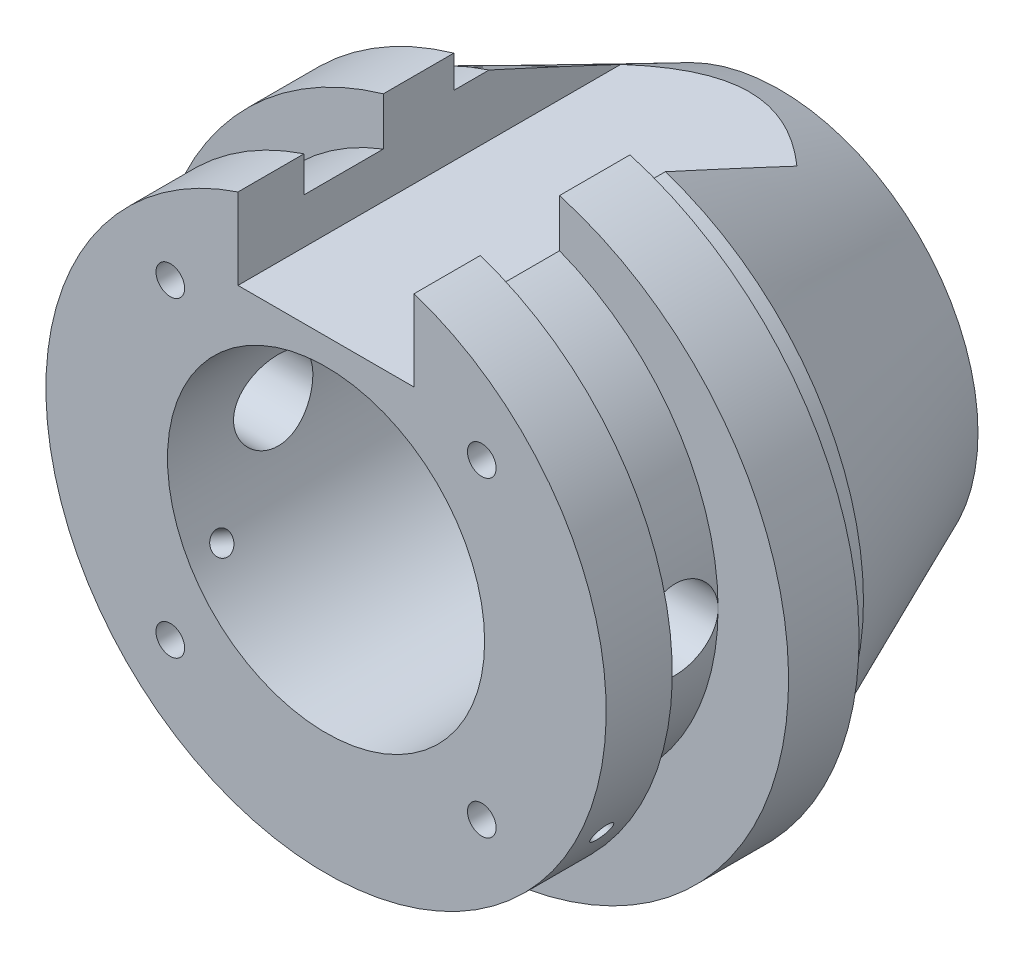
SolidWorks part; units mm, degrees
ref_plane "Plane1" through (0, 0, 0) normal (0, 0, 1) x (1, 0, 0)
ref_plane "Plane2" through (0, 0, 0) normal (0, 1, 0) x (1, 0, 0)
ref_plane "Plane3" through (0, 0, 0) normal (1, 0, 0) x (0, 0, -1)
sketch "Esquisse1" plane through (0, 0, 0) normal (0, 0, 1) x (1, 0, 0)
  circle A0 centre (0, 0) radius 36
  dimension "D1" = 72
extrude "Base-Extrusion" add sketch "Esquisse1" along normal blind 8
sketch "Esquisse2" plane through (0, 0, 0) normal (0, 0, -1) x (-1, 0, 0)
  circle A0 centre (0, 0) radius 32.5
  dimension "D1" = 65
extrude "Boss.-Extru.1" add sketch "Esquisse2" along normal blind 4
sketch "Esquisse3" plane through (0, 0, 0) normal (1, 0, 0) x (0, 0, -1)
  line L0 (4, 32.5) -> (27, 22.4993)
  line L1 (4, -32.5) -> (4, 32.5) construction
  line L2 (27, 22.4993) -> (27, 0)
  line L3 (0, 0) -> (39.1583, 0) construction
  line L4 (-8, 0) -> (0, 0) construction
  line L5 (4, 32.5) -> (4, 0)
  line L6 (4, 0) -> (27, 0)
  dimension "D1" = 23.5
  dimension "D2" = 23
revolve "Boss.-Révol.1" add sketch "Esquisse3" angle 360 about L3
sketch "Esquisse4" plane through (0, 0, 8) normal (0, 0, 1) x (1, 0, 0)
  line L0 (0, 0) -> (0, 21.3127) construction
  circle A0 centre (0, 3) radius 28
  dimension "D1" = 56
  dimension "D2" = 3
extrude "Boss.-Extru.2" add sketch "Esquisse4" along normal blind 9
sketch "Esquisse5" plane through (0, 0, 17) normal (0, 0, 1) x (1, 0, 0)
  circle A0 centre (0, 3) radius 31.8
  dimension "D1" = 63.6
extrude "Boss.-Extru.3" add sketch "Esquisse5" along normal blind 7.5
sketch "Esquisse6" plane through (0, 0, 24.5) normal (0, 0, 1) x (1, 0, 0)
  circle A0 centre (0, 3) radius 18
  dimension "D1" = 36
extrude "Enlèv. mat.-Extru.1" cut sketch "Esquisse6" against normal through all
sketch "Esquisse10" plane through (0, 0, 24.5) normal (0, 0, 1) x (1, 0, 0)
  line L0 (-10, 38.61) -> (10, 38.61)
  line L1 (-10, 38.61) -> (-10, 24)
  line L2 (10, 24) -> (-10, 24)
  line L3 (10, 24) -> (10, 38.61)
  line L4 (0, 0) -> (0, 38.61) construction
  line L5 (0, 3) -> (7.9537, 3) construction
  dimension "D1" = 21
  dimension "D2" = 20
extrude "Enlèv. mat.-Extru.5" cut sketch "Esquisse10" against normal through all
hole_wizard "Perçage1" positions "Esquisse12" profile "Esquisse11" legacy
sketch "Esquisse12" plane through (0, 0, 24.5) normal (0, 0, 1) x (1, 0, 0)
  line L0 (0, 3) -> (0, 12.7663) construction
  line L1 (0, 3) -> (22.3317, 3) construction
  line L2 (0, 3) -> (-17.6777, 20.6777) construction
  point P0 (-17.6777, 20.6777)
  dimension "D1" = 25
  dimension "D2" = 45
sketch "Esquisse11" plane through (-17.6777, 20.6777, 24.5) normal (1, 0, 0) x (0, -1, 0)
  line L0 (0, 0) -> (0, 12.9764)
  line L1 (0, 12.9764) -> (1.625, 12)
  line L2 (1.625, 12) -> (1.625, 0)
  line L4 (1.625, 0) -> (0, 0)
  line L6 (0, 12.9764) -> (-1.625, 12) construction
  line L7 (0, -4.2442) -> (0, 117.3081) construction
  dimension "Diamètre" = 3.25
  dimension "Profondeur" = 12
  dimension "Angle" = 118
cosmetic thread "Représentation de filetage1" parameters "D1"=8, "D2"=4
pattern_circular "Répétition circulaire1" count 4 every 90 about axis through (0, 3, 0) along (0, 0, 1) of "Perçage1"
sketch "Esquisse13" plane through (0, 0, 0) normal (1, 0, 0) x (0, 0, -1)
  line L0 (-17, 3) -> (-8, 3) construction
  line L3 (-12.5, 3) -> (-12.5, 14.8859) construction
  line L4 (-8, 34.5832) -> (-8, -36) construction
  line L5 (-17, -28.8) -> (-17, 33.1868) construction
  circle A0 centre (-12.5, 3) radius 4.5
  dimension "D1" = 9
extrude "Enlèv. mat.-Extru.6" cut sketch "Esquisse13" against normal through all and the other way through all
ref_plane "Plan4" through (-1.299, 0.75, 0) normal (-0.866, 0.5, 0) x (0, 0, 1)
sketch "Esquisse14" plane through (-1.299, 0.75, 0) normal (-0.866, 0.5, 0) x (0, 0, 1)
  line L0 (20.75, 2.5981) -> (20.75, 12.2528) construction
  line L1 (17, 2.5981) -> (8, 2.5981) construction
  line L2 (17, 34.3981) -> (17, -29.2019) construction
  line L3 (24.5, -29.2019) -> (24.5, 34.3981) construction
  circle A0 centre (20.75, 2.5981) radius 1.23
  dimension "D1" = 2.46
extrude "Enlèv. mat.-Extru.7" cut sketch "Esquisse14" against normal up to surface (31.7762 mm away)
cosmetic thread "Représentation de filetage2" parameters "D2"=3
pattern_circular "Répétition circulaire2" count 2 every 120 of "Enlèv. mat.-Extru.7"
